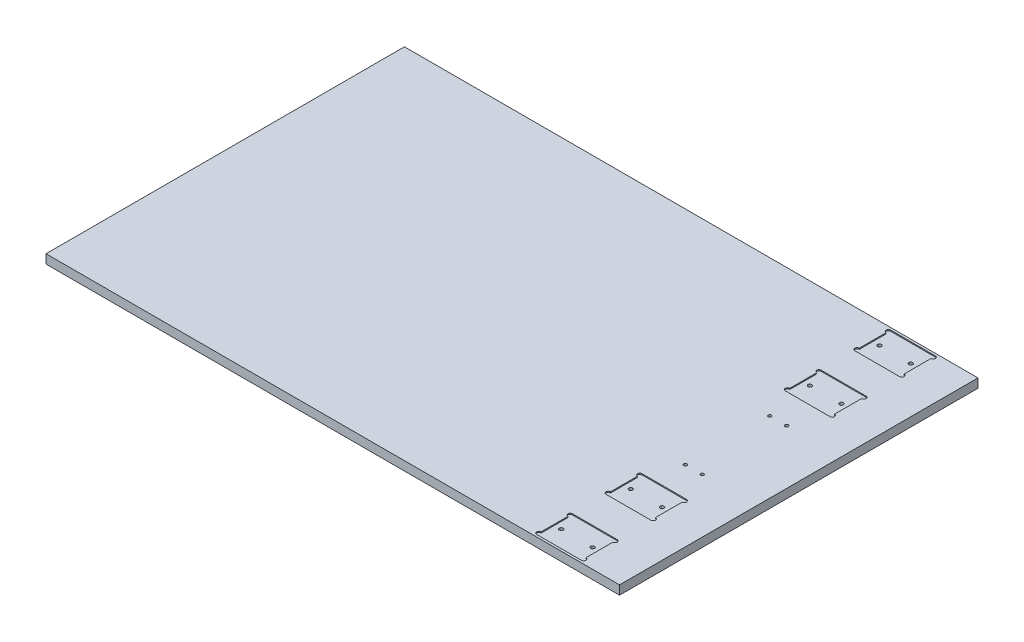
SolidWorks part; units mm, degrees
ref_plane "Front Plane" through (0, 0, 0) normal (0, 0, 1) x (1, 0, 0)
ref_plane "Top Plane" through (0, 0, 0) normal (0, 1, 0) x (1, 0, 0)
ref_plane "Right Plane" through (0, 0, 0) normal (1, 0, 0) x (0, 0, -1)
sketch "Sketch2" plane through (0, 0, 0) normal (0, 0, 1) x (1, 0, 0)
  line L1 (0, 0) -> (406.4, 0)
  line L2 (0, 0) -> (0, 6.35)
  line L3 (0, 6.35) -> (406.4, 6.35)
  line L4 (406.4, 0) -> (406.4, 6.35)
  dimension "D1" = 6.35
  dimension "D2" = 406.4
extrude "Boss-Extrude1" add sketch "Sketch2" against normal blind 254
sketch "Sketch3" plane through (0, 6.35, 0) normal (0, 1, 0) x (1, 0, 0)
  line L0 (361.95, 160.429) -> (361.95, 14.3119) construction
  line L1 (406.4, 254) -> (406.4, 0) construction
  line L4 (406.4, 254) -> (0, 254) construction
  line L5 (455.8137, 127) -> (-55.377, 127) construction
  circle A0 centre (350.8248, 239.7252) radius 1.3462
  circle A1 centre (373.0752, 239.7252) radius 1.3462
  circle A2 centre (373.0752, 190.5) radius 1.3462
  circle A3 centre (350.8248, 190.5) radius 1.3462
  circle A4 centre (355.9556, 156.9212) radius 1.1303
  circle A5 centre (367.9444, 156.9212) radius 1.1303
  circle A6 centre (367.9444, 97.0788) radius 1.1303
  circle A7 centre (355.9556, 97.0788) radius 1.1303
  circle A8 centre (373.0752, 63.5) radius 1.3462
  circle A9 centre (350.8248, 63.5) radius 1.3462
  circle A10 centre (350.8248, 14.2748) radius 1.3462
  circle A11 centre (373.0752, 14.2748) radius 1.3462
  dimension "D6" = 2.6924
  dimension "D7" = 2.6924
  dimension "D8" = 2.6924
  dimension "D9" = 2.6924
  dimension "D5" = 22.2504
  dimension "D11" = 22.2504
  dimension "D13" = 2.2606
  dimension "D14" = 2.2606
  dimension "D15" = 2.2606
  dimension "D16" = 2.2606
  dimension "D19" = 97.0788
  dimension "D23" = 156.9212
  dimension "D4" = 33.3248
  dimension "D10" = 33.3248
  dimension "D17" = 97.0788
  dimension "D18" = 156.9212
  dimension "D20" = 63.5
  dimension "D21" = 63.5
  dimension "D22" = 14.2748
extrude "Cut-Extrude1" cut sketch "Sketch3" against normal through all
cosmetic thread "Cosmetic Thread1" parameters "D2"=2.7178
cosmetic thread "Cosmetic Thread2" parameters "D2"=2.7178
cosmetic thread "Cosmetic Thread3" parameters "D2"=2.7178
cosmetic thread "Cosmetic Thread4" parameters "D2"=2.7178
cosmetic thread "Cosmetic Thread5" parameters "D2"=2.286
cosmetic thread "Cosmetic Thread6" parameters "D2"=2.286
cosmetic thread "Cosmetic Thread7" parameters "D2"=2.286
cosmetic thread "Cosmetic Thread8" parameters "D2"=2.286
sketch "Sketch4" plane through (0, 6.35, 0) normal (0, 1, 0) x (1, 0, 0)
  line L0 (434.9651, 127) -> (-24.8784, 127) construction
  line L1 (346.075, 252.4252) -> (377.825, 252.4252)
  line L2 (346.075, 249.2502) -> (346.075, 230.2002)
  line L3 (346.075, 227.0252) -> (377.825, 227.0252)
  line L4 (377.825, 249.2502) -> (377.825, 230.2002)
  line L5 (346.075, 203.2) -> (377.825, 203.2)
  line L6 (346.075, 200.025) -> (346.075, 180.975)
  line L7 (346.075, 177.8) -> (377.825, 177.8)
  line L8 (377.825, 200.025) -> (377.825, 180.975)
  line L9 (346.075, 4.7498) -> (346.075, 23.7998)
  line L10 (346.075, 1.5748) -> (377.825, 1.5748)
  line L11 (377.825, 4.7498) -> (377.825, 23.7998)
  line L12 (346.075, 26.9748) -> (377.825, 26.9748)
  line L13 (346.075, 53.975) -> (346.075, 73.025)
  line L14 (346.075, 76.2) -> (377.825, 76.2)
  line L15 (377.825, 53.975) -> (377.825, 73.025)
  line L16 (346.075, 50.8) -> (377.825, 50.8)
  circle A0 centre (350.8248, 239.7252) radius 1.3462 construction
  arc A1 (377.825, 249.2502) -> (377.825, 252.4252) centre (377.825, 250.8377) ccw
  arc A2 (377.825, 227.0252) -> (377.825, 230.2002) centre (377.825, 228.6127) ccw
  arc A3 (346.075, 252.4252) -> (346.075, 249.2502) centre (346.075, 250.8377) ccw
  arc A4 (346.075, 230.2002) -> (346.075, 227.0252) centre (346.075, 228.6127) ccw
  circle A5 centre (350.8248, 190.5) radius 1.3462 construction
  arc A6 (377.825, 200.025) -> (377.825, 203.2) centre (377.825, 201.6125) ccw
  arc A7 (377.825, 177.8) -> (377.825, 180.975) centre (377.825, 179.3875) ccw
  arc A8 (346.075, 203.2) -> (346.075, 200.025) centre (346.075, 201.6125) ccw
  arc A9 (346.075, 180.975) -> (346.075, 177.8) centre (346.075, 179.3875) ccw
  arc A10 (346.075, 23.7998) -> (346.075, 26.9748) centre (346.075, 25.3873) cw
  arc A11 (346.075, 1.5748) -> (346.075, 4.7498) centre (346.075, 3.1623) cw
  arc A12 (377.825, 4.7498) -> (377.825, 1.5748) centre (377.825, 3.1623) cw
  arc A13 (377.825, 26.9748) -> (377.825, 23.7998) centre (377.825, 25.3873) cw
  arc A14 (346.075, 50.8) -> (346.075, 53.975) centre (346.075, 52.3875) cw
  arc A15 (346.075, 73.025) -> (346.075, 76.2) centre (346.075, 74.6125) cw
  arc A16 (377.825, 76.2) -> (377.825, 73.025) centre (377.825, 74.6125) cw
  arc A17 (377.825, 53.975) -> (377.825, 50.8) centre (377.825, 52.3875) cw
  dimension "D3" = 12.7
  dimension "D6" = 3.175
  dimension "D8" = 3.175
  dimension "D10" = 3.175
  dimension "D12" = 3.175
  dimension "D17" = 3.175
  dimension "D18" = 3.175
  dimension "D19" = 3.175
  dimension "D20" = 3.175
  dimension "D1" = 31.75
  dimension "D2" = 25.4
  dimension "D4" = 4.7498
  dimension "D5" = 1.5875
  dimension "D7" = 1.5875
  dimension "D9" = 1.5875
  dimension "D11" = 1.5875
  dimension "D13" = 31.75
  dimension "D14" = 25.4
  dimension "D15" = 12.7
  dimension "D16" = 4.7498
  dimension "D21" = 1.5875
  dimension "D22" = 1.5875
  dimension "D23" = 1.5875
  dimension "D24" = 1.5875
extrude "Cut-Extrude3" cut sketch "Sketch4" against normal blind 0.762
